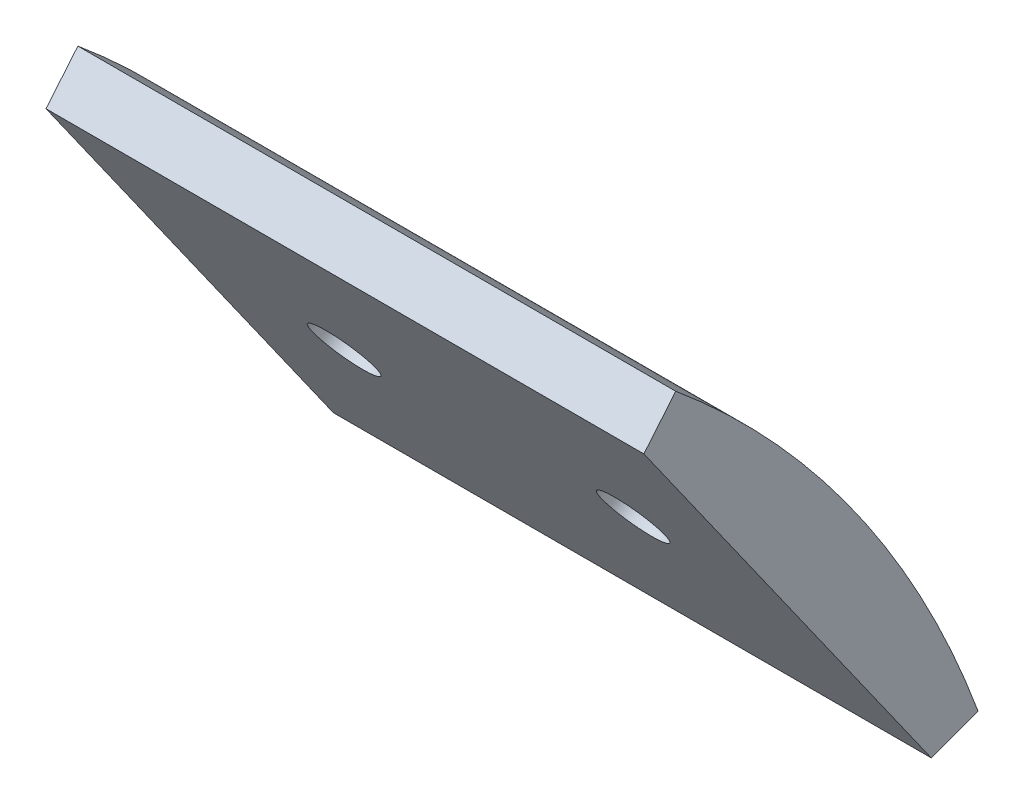
SolidWorks part; units mm, degrees
ref_plane "Front Plane" through (0, 0, 0) normal (0, 0, 1) x (1, 0, 0)
ref_plane "Top Plane" through (0, 0, 0) normal (0, 1, 0) x (1, 0, 0)
ref_plane "Right Plane" through (0, 0, 0) normal (1, 0, 0) x (0, 0, -1)
sketch "Sketch3" plane through (0, 0, 0) normal (1, 0, 0) x (0, 0, -1)
  line L0 (32.5, 39.0434) -> (30.9006, 37.122)
  line L1 (45.321, 16.7002) -> (47.6668, 17.5646)
  line L2 (32.5, 39.0434) -> (-32.5, 39.0434)
  line L3 (30.9006, 37.122) -> (45.321, 16.7002)
  circle A0 centre (0, 0) radius 50.8
  arc A1 (30.9006, 37.122) -> (45.321, 16.7002) centre (0, 0) cw
  dimension "D1" = 101.6
  dimension "D3" = 2.5
  dimension "D2" = 65
  dimension "D4" = 25
extrude "Boss-Extrude1" add sketch "Sketch3" along normal blind 30 contours L0 A1 L1 A0 | A1 L3
sketch "Sketch4" plane through (0, 26.9111, -38.1108) normal (0, -0.5768, 0.8169) x (1, 0, 0)
  line L0 (15, 12.5) -> (15, -12.5) construction
  line L4 (0, 12.5) -> (0, -12.5)
  line L5 (0, -12.5) -> (30, -12.5)
  line L6 (30, -12.5) -> (30, 12.5)
  line L7 (30, 12.5) -> (0, 12.5)
  line L8 (0, 12.5) -> (0, -12.5)
  line L9 (0, -12.5) -> (30, -12.5)
  line L10 (30, -12.5) -> (30, 12.5)
  line L11 (30, 12.5) -> (0, 12.5)
  circle A1 centre (7.75, 0) radius 1.605
  circle A2 centre (22.25, 0) radius 1.605
  dimension "D2" = 3.21
  dimension "D3" = 14.5
  dimension "D1" = 0
extrude "Cut-Extrude1" cut sketch "Sketch4" against normal up to surface (4.1202 mm away) contours A1 | A2
